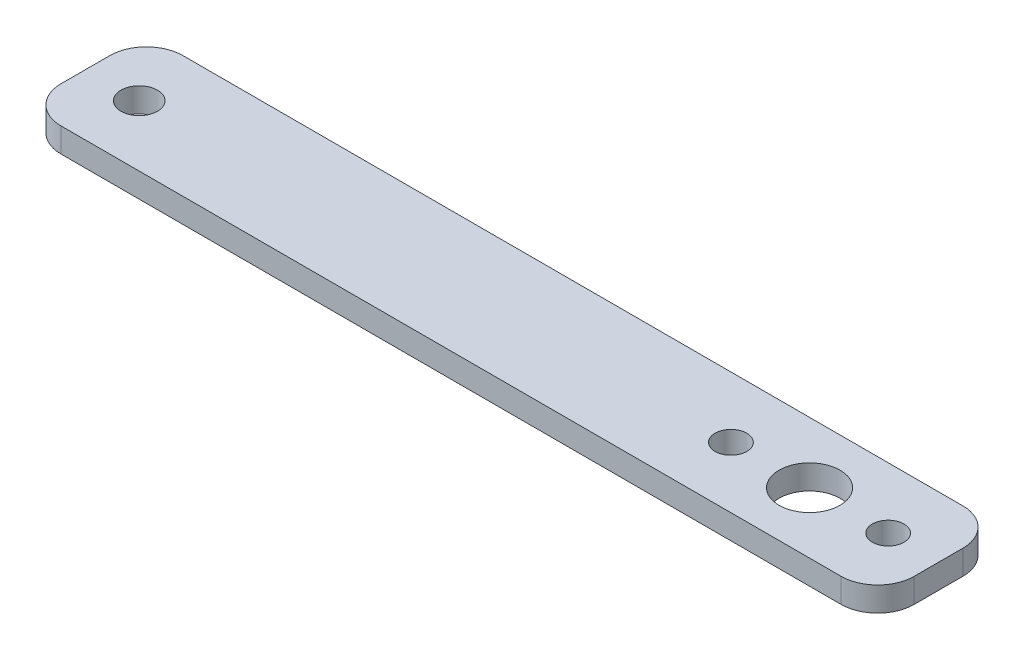
SolidWorks part; units mm, degrees
ref_plane "Front Plane" through (0, 0, 0) normal (0, 0, 1) x (1, 0, 0)
ref_plane "Top Plane" through (0, 0, 0) normal (0, 1, 0) x (1, 0, 0)
ref_plane "Right Plane" through (0, 0, 0) normal (1, 0, 0) x (0, 0, -1)
sketch "Sketch1" plane through (0, 0, 0) normal (0, 1, 0) x (1, 0, 0)
  line L1 (-35, 5) -> (35, 5)
  line L2 (-35, 5) -> (-35, -5)
  line L3 (-35, -5) -> (35, -5)
  line L4 (35, 5) -> (35, -5)
  line L5 (-35, 5) -> (35, -5) construction
  line L6 (-35, -5) -> (35, 5) construction
  point P0 (0, 0)
  dimension "D1" = 10
  dimension "D2" = 70
extrude "Boss-Extrude1" add sketch "Sketch1" along normal blind 2
hole_wizard "Ø5.0mm Dowel Hole1" positions "Sketch5" profile "Sketch6" hole size "Ø5.0" standard "ISO" end condition through all
sketch "Sketch5" plane through (0, 2, 0) normal (0, 1, 0) x (1, 0, 0)
  point P0 (24.4139, 0)
  point P3 (28.1142, 0)
  point P4 (23.2996, 0)
  point P5 (27.2939, 0)
  point P6 (24.4139, 0)
sketch "Sketch6" plane through (24.4139, 2, 0) normal (1, 0, 0) x (0, 0, 1)
  line L0 (0, 0) -> (0, 2)
  line L1 (0, 2) -> (2.5, 2)
  line L2 (2.5, 2) -> (2.5, 0)
  line L5 (2.5, 0) -> (0, 0)
  line L11 (0, -6.35) -> (0, 107.95) construction
  dimension "Thru Hole Dia." = 5
  dimension "Thru Hole Depth" = 2
hole_wizard "Ø3.0mm Dowel Hole1" positions "Sketch3" profile "Sketch4" hole size "Ø3.0" standard "ISO" end condition through all
sketch "Sketch3" plane through (0, 2, 0) normal (0, 1, 0) x (1, 0, 0)
  circle A0 centre (24.4139, 0) radius 2.5 construction
  point P0 (-30.5861, 0)
  dimension "D1" = 55
sketch "Sketch4" plane through (-30.5861, 2, 0) normal (1, 0, 0) x (0, 0, 1)
  line L0 (0, 0) -> (0, 2)
  line L1 (0, 2) -> (1.5, 2)
  line L2 (1.5, 2) -> (1.5, 0)
  line L5 (1.5, 0) -> (0, 0)
  line L11 (0, -6.35) -> (0, 107.95) construction
  dimension "Thru Hole Dia." = 3
  dimension "Thru Hole Depth" = 2
sketch "Sketch2" plane through (0, 2, 0) normal (0, 1, 0) x (1, 0, 0)
  line L0 (24.4139, 5) -> (24.4139, -5) construction
  line L1 (-35, -5) -> (35, -5) construction
  line L3 (35, 0) -> (-35, 0) construction
  line L4 (35, -5) -> (35, 5) construction
  line L5 (-35, 5) -> (-35, -5) construction
  circle A1 centre (30.8639, 0) radius 1.3
  circle A3 centre (17.9639, 0) radius 1.3
  point P10 (24.4139, 0)
  point P11 (-20.8705, -5.7016)
  point P15 (26.3156, 0)
  point P19 (0, 0)
  point P20 (27.2939, 0)
  dimension "D1" = 2.6
  dimension "D2" = 6.45
extrude "Cut-Extrude1" cut sketch "Sketch2" against normal blind 3
fillet "Fillet1" radius 3 4 edges at (35, 1, 5) (35, 1, -5) (-35, 1, -5) (-35, 1, 5)
equation "\"globalength1\"=55"
